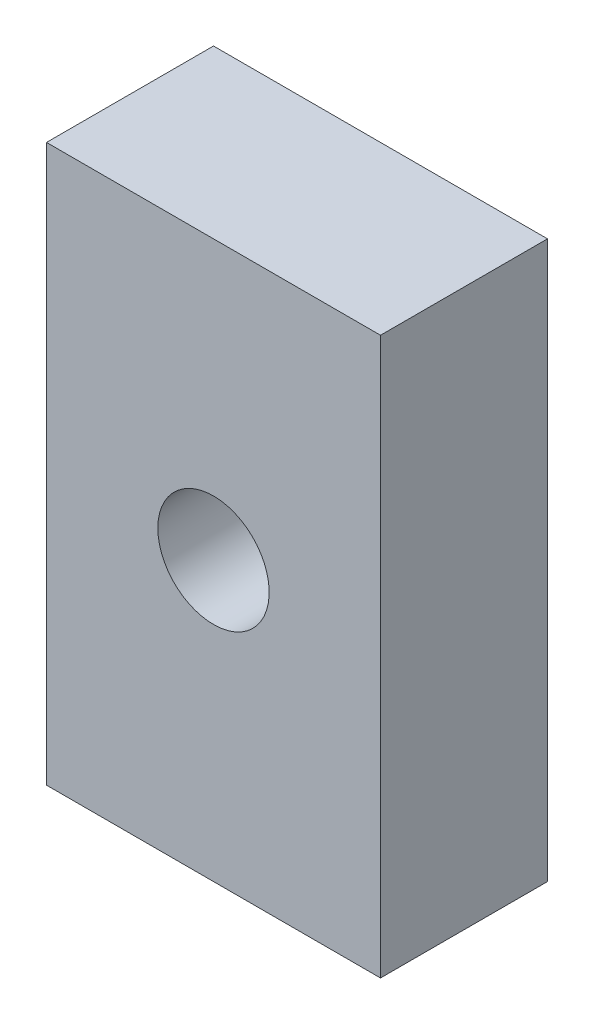
SolidWorks part; units mm, degrees
material "Plain Carbon Steel"
ref_plane "Front Plane" through (0, 0, 0) normal (0, 0, 1) x (1, 0, 0)
ref_plane "Top Plane" through (0, 0, 0) normal (0, 1, 0) x (1, 0, 0)
ref_plane "Right Plane" through (0, 0, 0) normal (1, 0, 0) x (0, 0, -1)
sketch "Sketch1" plane through (0, 0, 0) normal (0, 0, 1) x (1, 0, 0)
  line L1 (-19.05, -31.75) -> (19.05, -31.75)
  line L2 (-19.05, -31.75) -> (-19.05, 31.75)
  line L3 (-19.05, 31.75) -> (19.05, 31.75)
  line L4 (19.05, -31.75) -> (19.05, 31.75)
  line L5 (-19.05, -31.75) -> (19.05, 31.75) construction
  line L6 (-19.05, 31.75) -> (19.05, -31.75) construction
  point P0 (0, 0)
  dimension "D1" = 38.1
  dimension "D2" = 63.5
extrude "Extrude1" add sketch "Sketch1" along normal blind 19.05
hole_wizard "1/2 (0.5) Diameter Hole1" positions "Sketch4" profile "Sketch3" hole size "1/2" standard "Ansi Inch" end condition through all
sketch "Sketch4" plane through (0, 0, 0) normal (0, 0, -1) x (-1, 0, 0)
  point P1 (0, 0)
sketch "Sketch3" plane through (0, 0, 0) normal (1, 0, 0) x (0, 1, 0)
  line L0 (0, 0) -> (0, 19.05)
  line L1 (0, 19.05) -> (6.35, 19.05)
  line L2 (6.35, 19.05) -> (6.35, 0)
  line L5 (6.35, 0) -> (0, 0)
  line L11 (0, -6.35) -> (0, 107.95) construction
  dimension "Thru Hole Dia." = 12.7
  dimension "Thru Hole Depth" = 19.05
